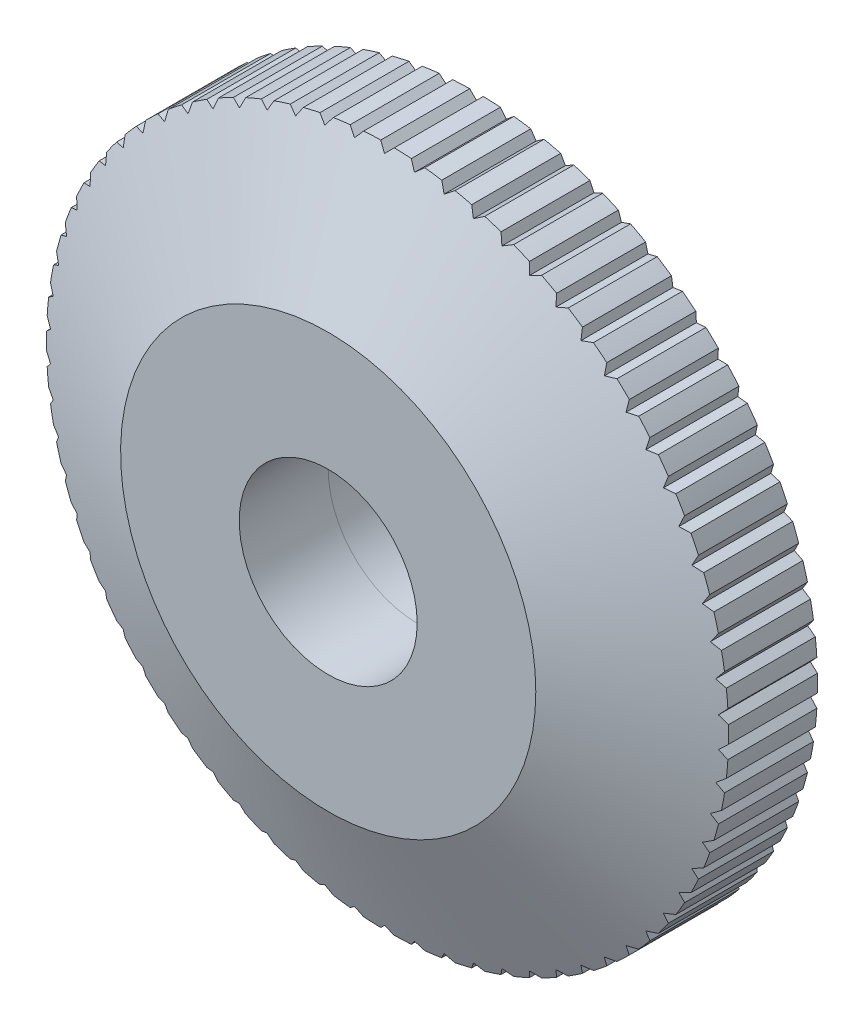
SolidWorks part; units mm, degrees
ref_plane "Спереди" through (0, 0, 0) normal (0, 0, 1) x (1, 0, 0)
ref_plane "Сверху" through (0, 0, 0) normal (0, 1, 0) x (1, 0, 0)
ref_plane "Справа" through (0, 0, 0) normal (1, 0, 0) x (0, 0, -1)
sketch "Эскиз1" plane through (0, 0, 0) normal (0, 0, 1) x (1, 0, 0)
  circle A0 centre (0, 0) radius 11.5
  dimension "D1" = 23
extrude "Бобышка-Вытянуть1" add sketch "Эскиз1" along normal blind 3
ref_plane "Плоскость1" through (0, 0, 5) normal (0, 0, 1) x (1, 0, 0)
sketch "Эскиз2" plane through (0, 0, 5) normal (0, 0, 1) x (1, 0, 0)
  circle A0 centre (0, 0) radius 7
  dimension "D1" = 14
sketch "Эскиз3" plane through (0, 0, 3) normal (0, 0, 1) x (1, 0, 0)
  circle A0 centre (0, 0) radius 11.5
  circle A1 centre (0, 0) radius 11.5 construction
loft "По сечениям2" add profiles "Эскиз2", "Эскиз3"
sketch "Эскиз4" plane through (0, 0, 0) normal (0, 0, -1) x (-1, 0, 0)
  circle A0 centre (0, 0) radius 10
  dimension "D1" = 20
extrude "Вырез-Вытянуть1" cut sketch "Эскиз4" against normal blind 2
sketch "Эскиз5" plane through (0, 0, 2) normal (0, 0, -1) x (-1, 0, 0)
  circle A0 centre (0, 0) radius 9.75
  dimension "D1" = 19.5
extrude "Бобышка-Вытянуть2" add sketch "Эскиз5" along normal blind 3 separate body
sketch "Эскиз6" plane through (0, 0, 0) normal (0, 0, -1) x (-1, 0, 0)
  line L0 (0, 11.5) -> (0, -11.5) construction
  line L1 (-0.2302, 11.5) -> (0, 11.2698)
  line L2 (0, 11.2698) -> (0.2302, 11.5)
  line L3 (0.2302, 11.5) -> (-0.2302, 11.5)
  line L4 (1.0102, 11.2244) -> (1.2601, 11.4331)
  line L5 (0.8016, 11.4743) -> (1.0102, 11.2244)
  line L6 (1.2601, 11.4331) -> (0.8016, 11.4743)
  line L7 (2.0123, 11.0887) -> (2.2799, 11.2741)
  line L8 (1.8269, 11.3563) -> (2.0123, 11.0887)
  line L9 (2.2799, 11.2741) -> (1.8269, 11.3563)
  line L10 (2.9982, 10.8637) -> (3.2813, 11.0243)
  line L11 (2.8375, 11.1468) -> (2.9982, 10.8637)
  line L12 (3.2813, 11.0243) -> (2.8375, 11.1468)
  line L13 (3.9599, 10.5512) -> (4.2563, 10.6858)
  line L14 (3.8253, 10.8476) -> (3.9599, 10.5512)
  line L15 (4.2563, 10.6858) -> (3.8253, 10.8476)
  line L16 (4.8898, 10.1537) -> (5.1971, 10.2613)
  line L17 (4.7823, 10.461) -> (4.8898, 10.1537)
  line L18 (5.1971, 10.2613) -> (4.7823, 10.461)
  line L19 (5.7803, 9.6745) -> (6.096, 9.7541)
  line L20 (5.7007, 9.9902) -> (5.7803, 9.6745)
  line L21 (6.096, 9.7541) -> (5.7007, 9.9902)
  line L22 (6.6242, 9.1175) -> (6.9458, 9.1684)
  line L23 (6.5733, 9.439) -> (6.6242, 9.1175)
  line L24 (6.9458, 9.1684) -> (6.5733, 9.439)
  line L25 (7.4148, 8.487) -> (7.7397, 8.5089)
  line L26 (7.3929, 8.8118) -> (7.4148, 8.487)
  line L27 (7.7397, 8.5089) -> (7.3929, 8.8118)
  line L28 (8.1457, 7.7881) -> (8.4712, 7.7808)
  line L29 (8.1531, 8.1136) -> (8.1457, 7.7881)
  line L30 (8.4712, 7.7808) -> (8.1531, 8.1136)
  line L31 (8.8111, 7.0266) -> (9.1346, 6.9901)
  line L32 (8.8475, 7.3501) -> (8.8111, 7.0266)
  line L33 (9.1346, 6.9901) -> (8.8475, 7.3501)
  line L34 (9.4055, 6.2085) -> (9.7244, 6.1432)
  line L35 (9.4708, 6.5274) -> (9.4055, 6.2085)
  line L36 (9.7244, 6.1432) -> (9.4708, 6.5274)
  line L37 (9.9241, 5.3404) -> (10.2359, 5.2468)
  line L38 (10.0178, 5.6522) -> (9.9241, 5.3404)
  line L39 (10.2359, 5.2468) -> (10.0178, 5.6522)
  line L40 (10.3629, 4.4293) -> (10.665, 4.3081)
  line L41 (10.4841, 4.7315) -> (10.3629, 4.4293)
  line L42 (10.665, 4.3081) -> (10.4841, 4.7315)
  line L43 (10.7182, 3.4826) -> (11.0083, 3.3348)
  line L44 (10.866, 3.7726) -> (10.7182, 3.4826)
  line L45 (11.0083, 3.3348) -> (10.866, 3.7726)
  line L46 (10.9872, 2.5078) -> (11.2629, 2.3346)
  line L47 (11.1604, 2.7834) -> (10.9872, 2.5078)
  line L48 (11.2629, 2.3346) -> (11.1604, 2.7834)
  line L49 (11.1678, 1.5128) -> (11.4268, 1.3156)
  line L50 (11.365, 1.7718) -> (11.1678, 1.5128)
  line L51 (11.4268, 1.3156) -> (11.365, 1.7718)
  line L52 (11.2584, 0.5056) -> (11.4987, 0.286)
  line L53 (11.4781, 0.7459) -> (11.2584, 0.5056)
  line L54 (11.4987, 0.286) -> (11.4781, 0.7459)
  line L55 (11.2584, -0.5056) -> (11.4781, -0.7459)
  line L56 (11.4987, -0.286) -> (11.2584, -0.5056)
  line L57 (11.4781, -0.7459) -> (11.4987, -0.286)
  line L58 (11.1678, -1.5128) -> (11.365, -1.7718)
  line L59 (11.4268, -1.3156) -> (11.1678, -1.5128)
  line L60 (11.365, -1.7718) -> (11.4268, -1.3156)
  line L61 (10.9872, -2.5078) -> (11.1604, -2.7834)
  line L62 (11.2629, -2.3346) -> (10.9872, -2.5078)
  line L63 (11.1604, -2.7834) -> (11.2629, -2.3346)
  line L64 (10.7182, -3.4826) -> (10.866, -3.7726)
  line L65 (11.0083, -3.3348) -> (10.7182, -3.4826)
  line L66 (10.866, -3.7726) -> (11.0083, -3.3348)
  line L67 (10.3629, -4.4293) -> (10.4841, -4.7315)
  line L68 (10.665, -4.3081) -> (10.3629, -4.4293)
  line L69 (10.4841, -4.7315) -> (10.665, -4.3081)
  line L70 (9.9241, -5.3404) -> (10.0178, -5.6522)
  line L71 (10.2359, -5.2468) -> (9.9241, -5.3404)
  line L72 (10.0178, -5.6522) -> (10.2359, -5.2468)
  line L73 (9.4055, -6.2085) -> (9.4708, -6.5274)
  line L74 (9.7244, -6.1432) -> (9.4055, -6.2085)
  line L75 (9.4708, -6.5274) -> (9.7244, -6.1432)
  line L76 (8.8111, -7.0266) -> (8.8475, -7.3501)
  line L77 (9.1346, -6.9901) -> (8.8111, -7.0266)
  line L78 (8.8475, -7.3501) -> (9.1346, -6.9901)
  line L79 (8.1457, -7.7881) -> (8.1531, -8.1136)
  line L80 (8.4712, -7.7808) -> (8.1457, -7.7881)
  line L81 (8.1531, -8.1136) -> (8.4712, -7.7808)
  line L82 (7.4148, -8.487) -> (7.3929, -8.8118)
  line L83 (7.7397, -8.5089) -> (7.4148, -8.487)
  line L84 (7.3929, -8.8118) -> (7.7397, -8.5089)
  line L85 (6.6242, -9.1175) -> (6.5733, -9.439)
  line L86 (6.9458, -9.1684) -> (6.6242, -9.1175)
  line L87 (6.5733, -9.439) -> (6.9458, -9.1684)
  line L88 (5.7803, -9.6745) -> (5.7007, -9.9902)
  line L89 (6.096, -9.7541) -> (5.7803, -9.6745)
  line L90 (5.7007, -9.9902) -> (6.096, -9.7541)
  line L91 (4.8898, -10.1537) -> (4.7823, -10.461)
  line L92 (5.1971, -10.2613) -> (4.8898, -10.1537)
  line L93 (4.7823, -10.461) -> (5.1971, -10.2613)
  line L94 (3.9599, -10.5512) -> (3.8253, -10.8476)
  line L95 (4.2563, -10.6858) -> (3.9599, -10.5512)
  line L96 (3.8253, -10.8476) -> (4.2563, -10.6858)
  line L97 (2.9982, -10.8637) -> (2.8375, -11.1468)
  line L98 (3.2813, -11.0243) -> (2.9982, -10.8637)
  line L99 (2.8375, -11.1468) -> (3.2813, -11.0243)
  line L100 (2.0123, -11.0887) -> (1.8269, -11.3563)
  line L101 (2.2799, -11.2741) -> (2.0123, -11.0887)
  line L102 (1.8269, -11.3563) -> (2.2799, -11.2741)
  line L103 (1.0102, -11.2244) -> (0.8016, -11.4743)
  line L104 (1.2601, -11.4331) -> (1.0102, -11.2244)
  line L105 (0.8016, -11.4743) -> (1.2601, -11.4331)
  line L106 (0, -11.2698) -> (-0.2302, -11.5)
  line L107 (0.2302, -11.5) -> (0, -11.2698)
  line L108 (-0.2302, -11.5) -> (0.2302, -11.5)
  line L109 (-1.0102, -11.2244) -> (-1.2601, -11.4331)
  line L110 (-0.8016, -11.4743) -> (-1.0102, -11.2244)
  line L111 (-1.2601, -11.4331) -> (-0.8016, -11.4743)
  line L112 (-2.0123, -11.0887) -> (-2.2799, -11.2741)
  line L113 (-1.8269, -11.3563) -> (-2.0123, -11.0887)
  line L114 (-2.2799, -11.2741) -> (-1.8269, -11.3563)
  line L115 (-2.9982, -10.8637) -> (-3.2813, -11.0243)
  line L116 (-2.8375, -11.1468) -> (-2.9982, -10.8637)
  line L117 (-3.2813, -11.0243) -> (-2.8375, -11.1468)
  line L118 (-3.9599, -10.5512) -> (-4.2563, -10.6858)
  line L119 (-3.8253, -10.8476) -> (-3.9599, -10.5512)
  line L120 (-4.2563, -10.6858) -> (-3.8253, -10.8476)
  line L121 (-4.8898, -10.1537) -> (-5.1971, -10.2613)
  line L122 (-4.7823, -10.461) -> (-4.8898, -10.1537)
  line L123 (-5.1971, -10.2613) -> (-4.7823, -10.461)
  line L124 (-5.7803, -9.6745) -> (-6.096, -9.7541)
  line L125 (-5.7007, -9.9902) -> (-5.7803, -9.6745)
  line L126 (-6.096, -9.7541) -> (-5.7007, -9.9902)
  line L127 (-6.6242, -9.1175) -> (-6.9458, -9.1684)
  line L128 (-6.5733, -9.439) -> (-6.6242, -9.1175)
  line L129 (-6.9458, -9.1684) -> (-6.5733, -9.439)
  line L130 (-7.4148, -8.487) -> (-7.7397, -8.5089)
  line L131 (-7.3929, -8.8118) -> (-7.4148, -8.487)
  line L132 (-7.7397, -8.5089) -> (-7.3929, -8.8118)
  line L133 (-8.1457, -7.7881) -> (-8.4712, -7.7808)
  line L134 (-8.1531, -8.1136) -> (-8.1457, -7.7881)
  line L135 (-8.4712, -7.7808) -> (-8.1531, -8.1136)
  line L136 (-8.8111, -7.0266) -> (-9.1346, -6.9901)
  line L137 (-8.8475, -7.3501) -> (-8.8111, -7.0266)
  line L138 (-9.1346, -6.9901) -> (-8.8475, -7.3501)
  line L139 (-9.4055, -6.2085) -> (-9.7244, -6.1432)
  line L140 (-9.4708, -6.5274) -> (-9.4055, -6.2085)
  line L141 (-9.7244, -6.1432) -> (-9.4708, -6.5274)
  line L142 (-9.9241, -5.3404) -> (-10.2359, -5.2468)
  line L143 (-10.0178, -5.6522) -> (-9.9241, -5.3404)
  line L144 (-10.2359, -5.2468) -> (-10.0178, -5.6522)
  line L145 (-10.3629, -4.4293) -> (-10.665, -4.3081)
  line L146 (-10.4841, -4.7315) -> (-10.3629, -4.4293)
  line L147 (-10.665, -4.3081) -> (-10.4841, -4.7315)
  line L148 (-10.7182, -3.4826) -> (-11.0083, -3.3348)
  line L149 (-10.866, -3.7726) -> (-10.7182, -3.4826)
  line L150 (-11.0083, -3.3348) -> (-10.866, -3.7726)
  line L151 (-10.9872, -2.5078) -> (-11.2629, -2.3346)
  line L152 (-11.1604, -2.7834) -> (-10.9872, -2.5078)
  line L153 (-11.2629, -2.3346) -> (-11.1604, -2.7834)
  line L154 (-11.1678, -1.5128) -> (-11.4268, -1.3156)
  line L155 (-11.365, -1.7718) -> (-11.1678, -1.5128)
  line L156 (-11.4268, -1.3156) -> (-11.365, -1.7718)
  line L157 (-11.2584, -0.5056) -> (-11.4987, -0.286)
  line L158 (-11.4781, -0.7459) -> (-11.2584, -0.5056)
  line L159 (-11.4987, -0.286) -> (-11.4781, -0.7459)
  line L160 (-11.2584, 0.5056) -> (-11.4781, 0.7459)
  line L161 (-11.4987, 0.286) -> (-11.2584, 0.5056)
  line L162 (-11.4781, 0.7459) -> (-11.4987, 0.286)
  line L163 (-11.1678, 1.5128) -> (-11.365, 1.7718)
  line L164 (-11.4268, 1.3156) -> (-11.1678, 1.5128)
  line L165 (-11.365, 1.7718) -> (-11.4268, 1.3156)
  line L166 (-10.9872, 2.5078) -> (-11.1604, 2.7834)
  line L167 (-11.2629, 2.3346) -> (-10.9872, 2.5078)
  line L168 (-11.1604, 2.7834) -> (-11.2629, 2.3346)
  line L169 (-10.7182, 3.4826) -> (-10.866, 3.7726)
  line L170 (-11.0083, 3.3348) -> (-10.7182, 3.4826)
  line L171 (-10.866, 3.7726) -> (-11.0083, 3.3348)
  line L172 (-10.3629, 4.4293) -> (-10.4841, 4.7315)
  line L173 (-10.665, 4.3081) -> (-10.3629, 4.4293)
  line L174 (-10.4841, 4.7315) -> (-10.665, 4.3081)
  line L175 (-9.9241, 5.3404) -> (-10.0178, 5.6522)
  line L176 (-10.2359, 5.2468) -> (-9.9241, 5.3404)
  line L177 (-10.0178, 5.6522) -> (-10.2359, 5.2468)
  line L178 (-9.4055, 6.2085) -> (-9.4708, 6.5274)
  line L179 (-9.7244, 6.1432) -> (-9.4055, 6.2085)
  line L180 (-9.4708, 6.5274) -> (-9.7244, 6.1432)
  line L181 (-8.8111, 7.0266) -> (-8.8475, 7.3501)
  line L182 (-9.1346, 6.9901) -> (-8.8111, 7.0266)
  line L183 (-8.8475, 7.3501) -> (-9.1346, 6.9901)
  line L184 (-8.1457, 7.7881) -> (-8.1531, 8.1136)
  line L185 (-8.4712, 7.7808) -> (-8.1457, 7.7881)
  line L186 (-8.1531, 8.1136) -> (-8.4712, 7.7808)
  line L187 (-7.4148, 8.487) -> (-7.3929, 8.8118)
  line L188 (-7.7397, 8.5089) -> (-7.4148, 8.487)
  line L189 (-7.3929, 8.8118) -> (-7.7397, 8.5089)
  line L190 (-6.6242, 9.1175) -> (-6.5733, 9.439)
  line L191 (-6.9458, 9.1684) -> (-6.6242, 9.1175)
  line L192 (-6.5733, 9.439) -> (-6.9458, 9.1684)
  line L193 (-5.7803, 9.6745) -> (-5.7007, 9.9902)
  line L194 (-6.096, 9.7541) -> (-5.7803, 9.6745)
  line L195 (-5.7007, 9.9902) -> (-6.096, 9.7541)
  line L196 (-4.8898, 10.1537) -> (-4.7823, 10.461)
  line L197 (-5.1971, 10.2613) -> (-4.8898, 10.1537)
  line L198 (-4.7823, 10.461) -> (-5.1971, 10.2613)
  line L199 (-3.9599, 10.5512) -> (-3.8253, 10.8476)
  line L200 (-4.2563, 10.6858) -> (-3.9599, 10.5512)
  line L201 (-3.8253, 10.8476) -> (-4.2563, 10.6858)
  line L202 (-2.9982, 10.8637) -> (-2.8375, 11.1468)
  line L203 (-3.2813, 11.0243) -> (-2.9982, 10.8637)
  line L204 (-2.8375, 11.1468) -> (-3.2813, 11.0243)
  line L205 (-2.0123, 11.0887) -> (-1.8269, 11.3563)
  line L206 (-2.2799, 11.2741) -> (-2.0123, 11.0887)
  line L207 (-1.8269, 11.3563) -> (-2.2799, 11.2741)
  line L208 (-1.0102, 11.2244) -> (-0.8016, 11.4743)
  line L209 (-1.2601, 11.4331) -> (-1.0102, 11.2244)
  line L210 (-0.8016, 11.4743) -> (-1.2601, 11.4331)
  circle A0 centre (0, 0) radius 11.5 construction
  point P219 (0, 0)
  dimension "D1" = 45
  dimension "D3" = 70
extrude "Вырез-Вытянуть2" cut sketch "Эскиз6" against normal through all
sketch "Эскиз8" plane through (0, 0, 5) normal (0, 0, 1) x (1, 0, 0)
  circle A0 centre (0, 0) radius 3
  dimension "D1" = 6
extrude "Вырез-Вытянуть3" cut sketch "Эскиз8" against normal through all
